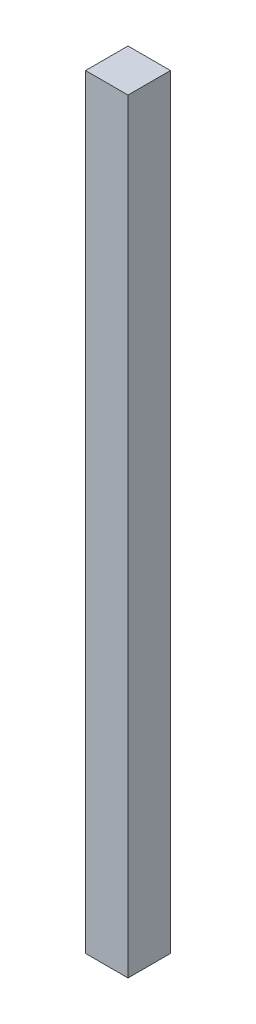
SolidWorks part; units mm, degrees
material "AISI 304"
ref_plane "Front Plane" through (0, 0, 0) normal (0, 0, 1) x (1, 0, 0)
ref_plane "Top Plane" through (0, 0, 0) normal (0, 1, 0) x (1, 0, 0)
ref_plane "Right Plane" through (0, 0, 0) normal (1, 0, 0) x (0, 0, -1)
sketch "Sketch1" plane through (0, 0, 0) normal (0, 1, 0) x (1, 0, 0)
  line L1 (0, 0) -> (25.4, 0)
  line L2 (0, 0) -> (0, 25.4)
  line L3 (0, 25.4) -> (25.4, 25.4)
  line L4 (25.4, 0) -> (25.4, 25.4)
  dimension "D1" = 25.4
  dimension "D2" = 25.4
extrude "Boss-Extrude1" add sketch "Sketch1" against normal blind 457.2
